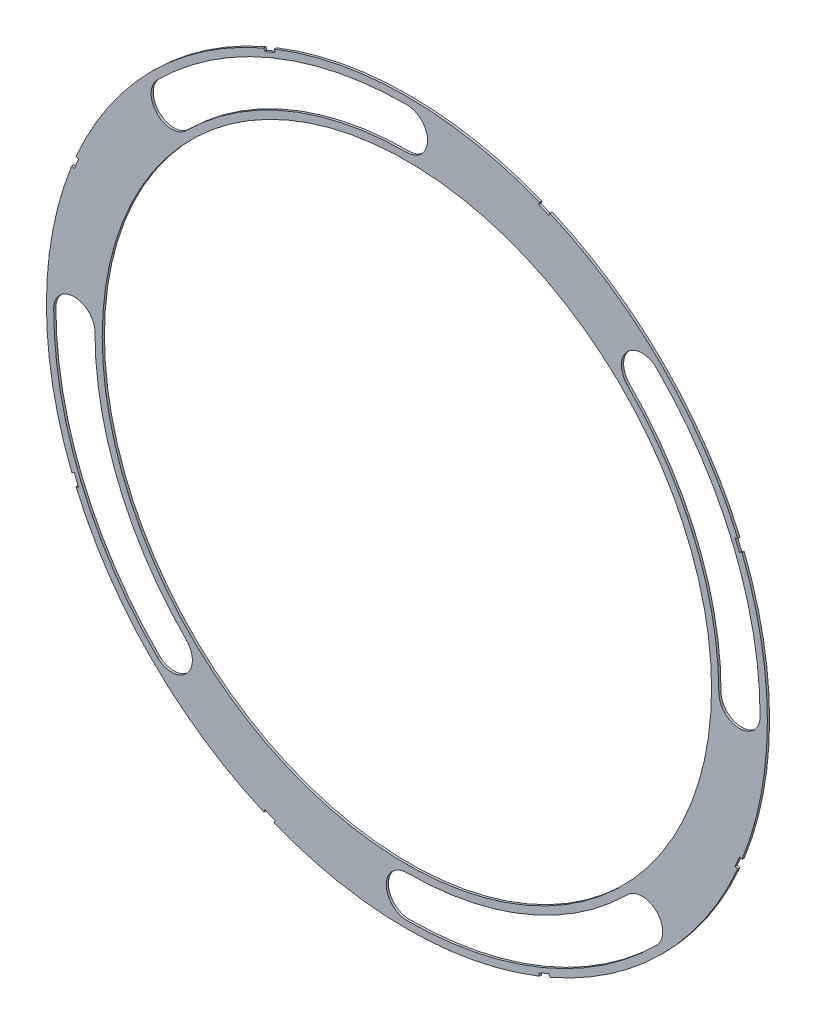
SolidWorks part; units mm, degrees
material "PTFE (general)"
ref_plane "Front Plane" through (0, 0, 0) normal (0, 0, 1) x (1, 0, 0)
ref_plane "Top Plane" through (0, 0, 0) normal (0, 1, 0) x (1, 0, 0)
ref_plane "Right Plane" through (0, 0, 0) normal (1, 0, 0) x (0, 0, -1)
sketch "Sketch4" plane through (0, 0, 0) normal (0, 0, 1) x (1, 0, 0)
  circle A0 centre (0, 0) radius 82.042
  dimension "D1" = 164.084
extrude "Boss-Extrude2" add sketch "Sketch4" along normal blind 0.508
sketch "Sketch5" plane through (0, 0, 0.508) normal (0, 0, 1) x (1, 0, 0)
  circle A0 centre (0, 0) radius 69.342
  circle A1 centre (0, 0) radius 82.042 construction
  dimension "D1" = 12.7
extrude "Cut-Extrude5" cut sketch "Sketch5" against normal through all
sketch "Sketch6" plane through (0, 0, 0.508) normal (0, 0, 1) x (1, 0, 0)
  line L0 (0, 0) -> (36.195, 0) construction
  line L1 (0, 0) -> (58.0125, -58.0125) construction
  line L2 (0, 0) -> (0, -82.042) construction
  line L3 (0, 0) -> (0, -82.042) construction
  line L4 (0, 0) -> (58.0125, -58.0125) construction
  line L5 (0, 0) -> (-58.0125, -58.0125) construction
  line L6 (0, 0) -> (-58.0125, -58.0125) construction
  line L7 (0, 0) -> (-82.042, 0) construction
  line L8 (0, 0) -> (-82.042, 0) construction
  line L9 (0, 0) -> (-58.0125, 58.0125) construction
  line L10 (0, 0) -> (-58.0125, 58.0125) construction
  line L11 (0, 0) -> (0, 82.042) construction
  line L12 (0, 0) -> (0, 82.042) construction
  line L13 (0, 0) -> (50.1996, -50.1996) construction
  line L14 (0, 0) -> (-50.1996, -50.1996) construction
  line L15 (0, 0) -> (58.0125, 58.0125) construction
  line L16 (0, 0) -> (58.0125, 58.0125) construction
  line L17 (0, 0) -> (82.042, 0) construction
  line L18 (0, 0) -> (82.042, 0) construction
  arc A0 (56.845, 56.845) -> (50.1996, 50.1996) centre (53.5223, 53.5223) ccw
  circle A1 centre (0, 0) radius 82.042 construction
  arc A2 (56.845, -56.845) -> (50.1996, -50.1996) centre (53.5223, -53.5223) ccw
  arc A3 (50.1996, -50.1996) -> (0, -70.993) centre (0, 0) cw
  arc A4 (0, -70.993) -> (0, -80.391) centre (0, -75.692) ccw
  arc A5 (0, -80.391) -> (56.845, -56.845) centre (0, 0) ccw
  arc A6 (-56.845, -56.845) -> (-50.1996, -50.1996) centre (-53.5223, -53.5223) ccw
  arc A7 (-50.1996, -50.1996) -> (-70.993, 0) centre (0, 0) cw
  arc A8 (-80.391, 0) -> (-56.845, -56.845) centre (0, 0) ccw
  arc A9 (-70.993, 0) -> (-80.391, 0) centre (-75.692, 0) ccw
  arc A10 (-56.845, 56.845) -> (-50.1996, 50.1996) centre (-53.5223, 53.5223) ccw
  arc A11 (-50.1996, 50.1996) -> (0, 70.993) centre (0, 0) cw
  arc A12 (0, 80.391) -> (-56.845, 56.845) centre (0, 0) ccw
  arc A13 (0, 70.993) -> (0, 80.391) centre (0, 75.692) ccw
  arc A14 (50.1996, 50.1996) -> (70.993, 0) centre (0, 0) cw
  arc A15 (80.391, 0) -> (56.845, 56.845) centre (0, 0) ccw
  circle A16 centre (0, 0) radius 69.342 construction
  arc A17 (70.993, 0) -> (80.391, 0) centre (75.692, 0) ccw
  point P4 (53.5223, -53.5223)
  point P11 (0, -75.692)
  point P13 (-53.5223, -53.5223)
  point P22 (53.5223, 53.5223)
  point P27 (-75.692, 0)
  point P30 (0, 0)
  point P36 (-53.5223, 53.5223)
  point P41 (0, 75.692)
  point P55 (75.692, 0)
  dimension "D2" = 4
  dimension "D3" = 45
  dimension "D4" = 90
  dimension "D6" = 6.35
  dimension "D7" = 9.398
  dimension "D8" = 4.699
  dimension "D9" = 4.699
  dimension "D5" = 6.35
  dimension "D10" = 90
extrude "Cut-Extrude6" cut sketch "Sketch6" against normal through all
sketch "Sketch8" plane through (0, 0, 0.508) normal (0, 0, 1) x (1, 0, 0)
  line L2 (76.8696, 30.4658) -> (75.8976, 32.8124)
  line L3 (76.8696, 30.4658) -> (75.6963, 29.9798)
  line L4 (75.6963, 29.9798) -> (74.7243, 32.3264)
  line L5 (75.8976, 32.8124) -> (74.7243, 32.3264)
  line L6 (0, 0) -> (82.042, 0) construction
  line L7 (-30.4658, 76.8696) -> (-32.8124, 75.8976)
  line L8 (-30.4658, 76.8696) -> (-29.9798, 75.6963)
  line L9 (-32.8124, 75.8976) -> (-32.3264, 74.7243)
  line L10 (-29.9798, 75.6963) -> (-32.3264, 74.7243)
  line L11 (-32.8124, 75.8976) -> (-29.9798, 75.6963) construction
  line L12 (-30.4658, 76.8696) -> (-32.3264, 74.7243) construction
  line L13 (-75.8976, 32.8124) -> (-76.8696, 30.4658)
  line L14 (-75.8976, 32.8124) -> (-74.7243, 32.3264)
  line L15 (-74.7243, 32.3264) -> (-75.6963, 29.9798)
  line L16 (-76.8696, 30.4658) -> (-75.6963, 29.9798)
  line L17 (-75.8976, 32.8124) -> (-75.6963, 29.9798) construction
  line L18 (-76.8696, 30.4658) -> (-74.7243, 32.3264) construction
  line L19 (-76.8696, -30.4658) -> (-75.8976, -32.8124)
  line L20 (-76.8696, -30.4658) -> (-75.6963, -29.9798)
  line L21 (-75.6963, -29.9798) -> (-74.7243, -32.3264)
  line L22 (-75.8976, -32.8124) -> (-74.7243, -32.3264)
  line L23 (-76.8696, -30.4658) -> (-74.7243, -32.3264) construction
  line L24 (-75.8976, -32.8124) -> (-75.6963, -29.9798) construction
  line L25 (-32.8124, -75.8976) -> (-30.4658, -76.8696)
  line L26 (-32.8124, -75.8976) -> (-32.3264, -74.7243)
  line L27 (-32.3264, -74.7243) -> (-29.9798, -75.6963)
  line L28 (-30.4658, -76.8696) -> (-29.9798, -75.6963)
  line L29 (-32.8124, -75.8976) -> (-29.9798, -75.6963) construction
  line L30 (-30.4658, -76.8696) -> (-32.3264, -74.7243) construction
  line L31 (30.4658, -76.8696) -> (32.8124, -75.8976)
  line L32 (30.4658, -76.8696) -> (29.9798, -75.6963)
  line L33 (29.9798, -75.6963) -> (32.3264, -74.7243)
  line L34 (32.8124, -75.8976) -> (32.3264, -74.7243)
  line L35 (30.4658, -76.8696) -> (32.3264, -74.7243) construction
  line L36 (32.8124, -75.8976) -> (29.9798, -75.6963) construction
  line L37 (75.8976, -32.8124) -> (76.8696, -30.4658)
  line L38 (75.8976, -32.8124) -> (74.7243, -32.3264)
  line L39 (74.7243, -32.3264) -> (75.6963, -29.9798)
  line L40 (76.8696, -30.4658) -> (75.6963, -29.9798)
  line L41 (75.8976, -32.8124) -> (75.6963, -29.9798) construction
  line L42 (76.8696, -30.4658) -> (74.7243, -32.3264) construction
  line L43 (76.8696, 30.4658) -> (74.7243, 32.3264) construction
  line L44 (75.8976, 32.8124) -> (75.6963, 29.9798) construction
  line L45 (32.8124, 75.8976) -> (30.4658, 76.8696)
  line L46 (32.8124, 75.8976) -> (32.3264, 74.7243)
  line L47 (32.3264, 74.7243) -> (29.9798, 75.6963)
  line L48 (30.4658, 76.8696) -> (29.9798, 75.6963)
  line L49 (32.8124, 75.8976) -> (29.9798, 75.6963) construction
  line L50 (30.4658, 76.8696) -> (32.3264, 74.7243) construction
  circle A0 centre (0, 0) radius 82.042 construction
  point P3 (-31.3961, 75.7969)
  point P11 (-75.7969, 31.3961)
  point P15 (75.7969, 31.3961)
  point P20 (-75.7969, -31.3961)
  point P25 (-31.3961, -75.7969)
  point P26 (0, 0)
  point P31 (31.3961, -75.7969)
  point P36 (75.7969, -31.3961)
  point P45 (31.3961, 75.7969)
  point P46 (0, 0)
  dimension "D3" = 0.635
  dimension "D5" = 1.27
  dimension "D6" = 2.54
  dimension "D7" = 1.27
  dimension "D9" = 0.635
  dimension "D10" = 112.5
  dimension "D14" = 0.635
  dimension "D21" = 22.5
  dimension "D11" = 8
extrude "Cut-Extrude11" cut sketch "Sketch8" against normal through all
